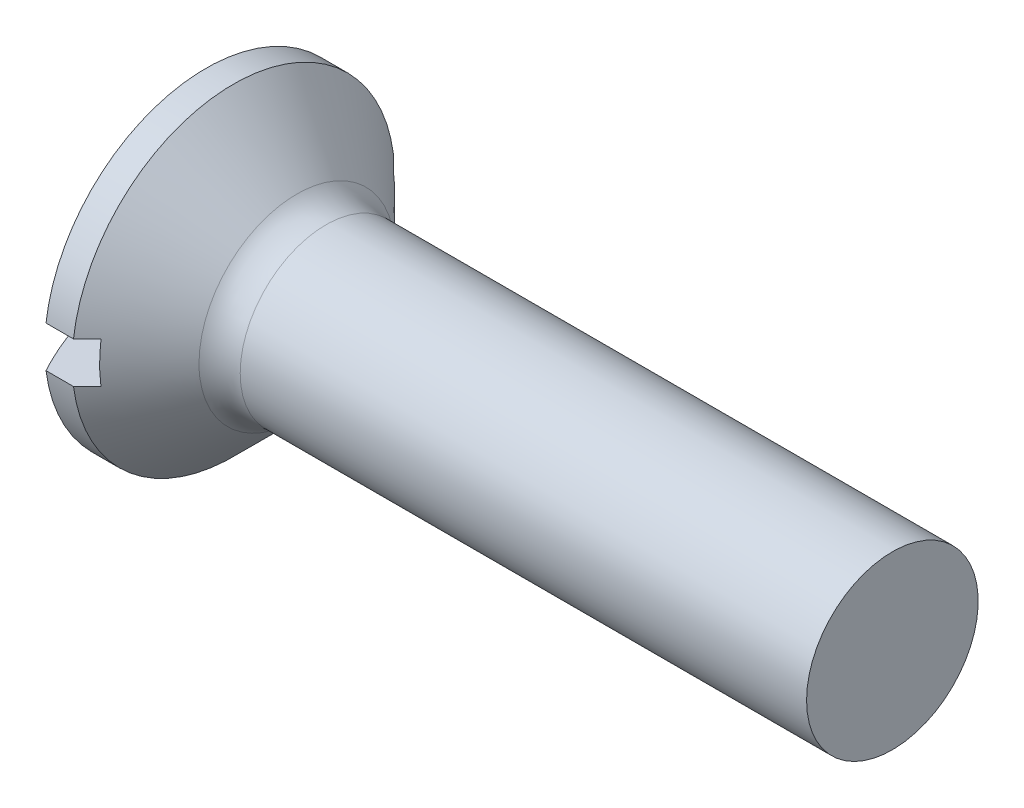
SolidWorks part; units mm, degrees
ref_plane "Plane1" through (0, 0, 0) normal (0, 0, 1) x (1, 0, 0)
ref_plane "Plane2" through (0, 0, 0) normal (0, 1, 0) x (1, 0, 0)
ref_plane "Plane3" through (0, 0, 0) normal (1, 0, 0) x (0, 0, -1)
sketch "BodySke" plane through (0, 0, 0) normal (0, 0, 1) x (1, 0, 0)
  line L0 (0, 0) -> (10.6, 0)
  line L1 (10.6, 0) -> (10.6, 1.25)
  line L2 (10.6, 1.25) -> (2.1, 1.25)
  line L3 (1, -2.35) -> (2.1, -1.25) construction
  line L4 (-15.875, 0) -> (82.55, 0) construction
  line L5 (1, 2.35) -> (2.1, 1.25)
  line L6 (2.55, 4.425) -> (2.55, -11.45) construction
  line L7 (0.6, 2.7793) -> (0.6, -13.0957) construction
  line L8 (1, 2.35) -> (0.6, 2.35)
  arc A0 (0, 0) -> (0.6, 2.35) centre (4.9021, 0) cw
  dimension "Length" = 10
  dimension "Diameter" = 2.5
  dimension "Head_dia" = 4.7
  dimension "Head_ang" = 90
  dimension "Advance" = 0.45
  dimension "Thread_nom" = 10
  dimension "Oval_ht" = 0.6
  dimension "Side_ht" = 1.5
revolve "Base-Revolve" add sketch "BodySke"
cosmetic thread "ThreadCosmetic"
extrude "Slot" cut sketch "Sketch2" along normal blind 1.2
sketch "Sketch2" plane through (0, 0, 0) normal (1, 0, 0) x (0, 0, -1)
  line L0 (2.35, -0.3) -> (-2.35, -0.3)
  line L1 (2.35, -0.3) -> (2.35, 0.3)
  line L2 (-2.35, 0.3) -> (2.35, 0.3)
  line L3 (-2.35, 0.3) -> (-2.35, -0.3)
  dimension "D1" = 4.7
  dimension "Slot_width" = 0.6
  dimension "D3" = 2.35
  dimension "D4" = 0.3
fillet "Fillet1" radius 0.6 1 edges at (2.1, 0, 1.25)
sketch "ThdSchSke" plane through (0, 0, 0) normal (0, 0, 1) x (1, 0, 0)
  line L0 (2.55, -0.9965) -> (2.3725, -1.25)
  line L1 (2.55, -0.9965) -> (2.7275, -1.25)
  line L2 (2.7275, -1.25) -> (2.7275, -1.5625)
  line L3 (-3.175, 0) -> (5.1513, 0) construction
  line L5 (2.7275, -1.5625) -> (2.3725, -1.5625)
  line L6 (2.3725, -1.5625) -> (2.3725, -1.25)
  dimension "Thread_minor" = 1.993
  dimension "Diameter" = 2.5
  dimension "Start" = 2.55
  dimension "SideAngle" = 55
  dimension "VeeAngle" = 70
  dimension "Overcut" = 3.125
revolve "ThreadSchematic" [suppressed] cut sketch "ThdSchSke" angle 360 about L3
pattern_linear "ThdSchPat" [suppressed]
equation "\"D1@Sketch2\" = \"Head_dia@BodySke\""
equation "\"D3@Sketch2\" = \"D1@Sketch2\" / 2"
equation "\"D4@Sketch2\" = \"Slot_width@Sketch2\" / 2"
equation "\"Thread_length@ThreadCosmetic\" = ((sgn( (\"Length@BodySke\" - \"Advance@BodySke\" - \"Side_ht@BodySke\" ) - \"Thread_nom@BodySke\" )-1)*( (\"Length@BodySke\" - \"Advance@BodySke\" - \"Side_ht@BodySke\" ) - \"Thread_nom@BodySke\" ))/-2+ \"Thread_nom@BodySke\""
equation "\"Thread_minor@ThdSchSke\" = \"Thread_minor@ThreadCosmetic\""
equation "\"Diameter@ThdSchSke\" = \"Diameter@BodySke\""
equation "\"Overcut@ThdSchSke\" = \"Diameter@BodySke\" * 1.25"
equation "\"Start@ThdSchSke\" = \"Oval_ht@BodySke\" + \"Length@BodySke\" - \"Thread_length@ThreadCosmetic\"  '---Countersunk---"
equation "\"Num_threads@ThdSchPat\" = int( \"Thread_length@ThreadCosmetic\" / \"Advance@BodySke\" + 0.999 )  + 1"
equation "\"Advance@ThdSchPat\" = \"Thread_length@ThreadCosmetic\" /  (\"Num_threads@ThdSchPat\" - 1) 'relax it"
